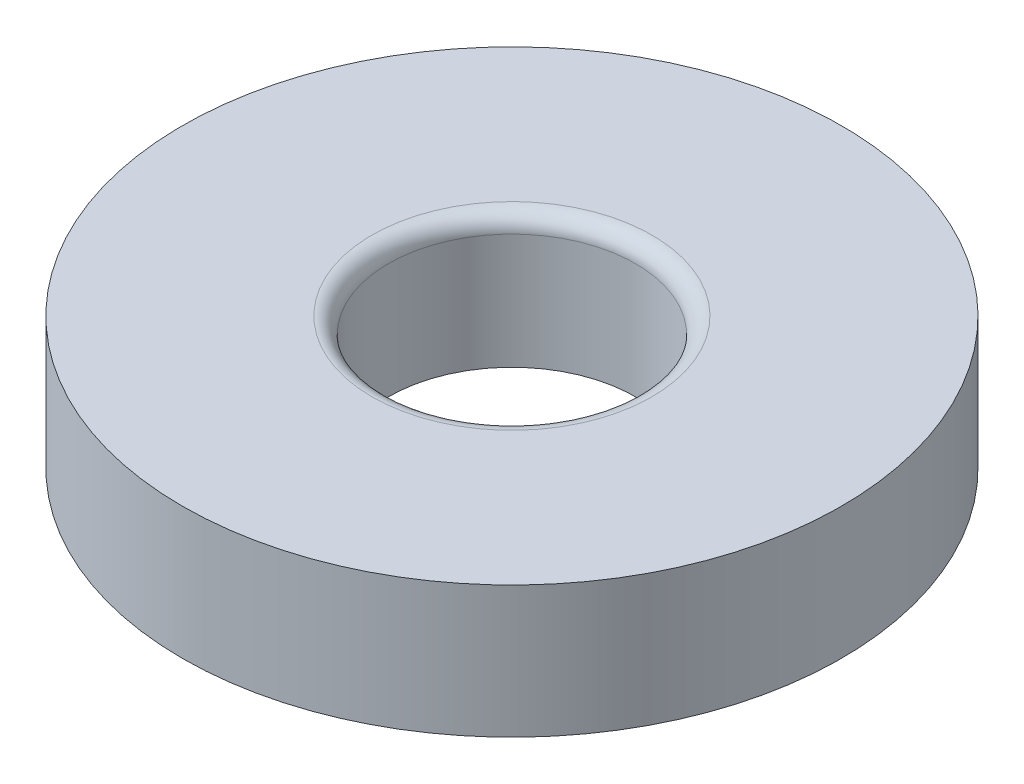
SolidWorks part; units mm, degrees
ref_plane "Front Plane" through (0, 0, 0) normal (0, 0, 1) x (1, 0, 0)
ref_plane "Top Plane" through (0, 0, 0) normal (0, 1, 0) x (1, 0, 0)
ref_plane "Right Plane" through (0, 0, 0) normal (1, 0, 0) x (0, 0, -1)
sketch "Sketch1" plane through (0, 0, 0) normal (0, 1, 0) x (1, 0, 0)
  circle A0 centre (0, 0) radius 20
extrude "Boss-Extrude1" add sketch "Sketch1" along normal blind 8 separate body
sketch "Sketch2" plane through (0, 8, 0) normal (0, 1, 0) x (1, 0, 0)
  circle A0 centre (0, 0) radius 7.5
extrude "Cut-Extrude1" cut sketch "Sketch2" against normal through all
fillet "Fillet1" radius 1 1 edges at (0, 8, 7.5)
